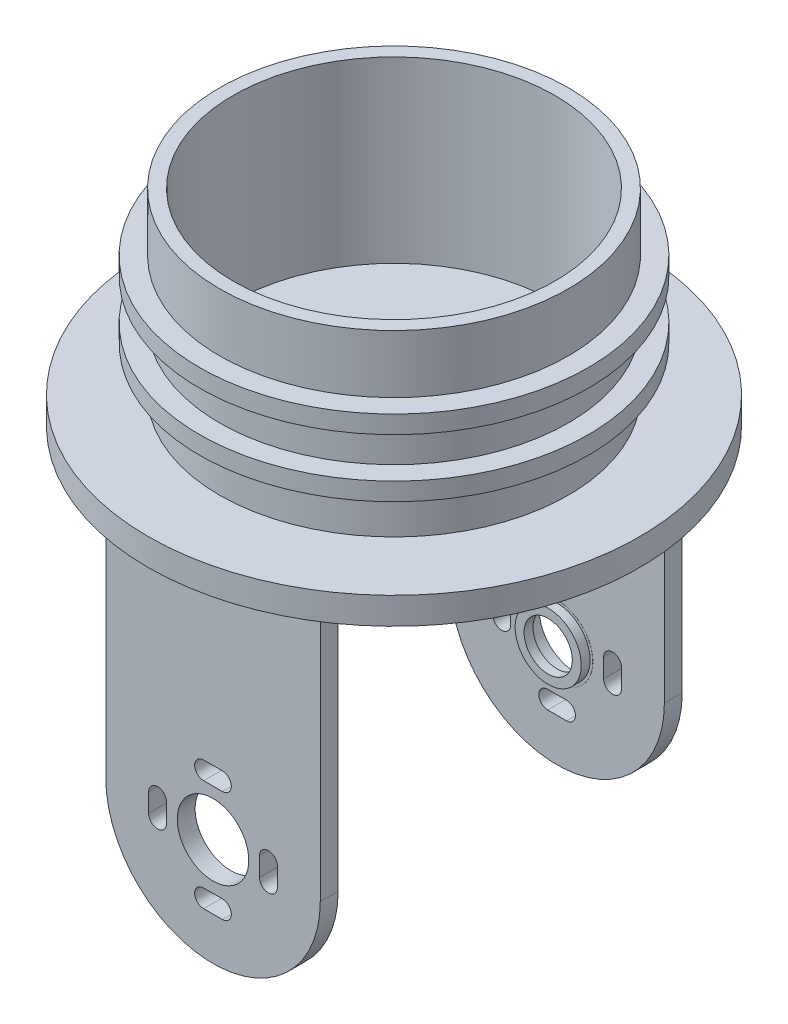
SolidWorks part; units mm, degrees
ref_plane "前基準面" through (0, 0, 0) normal (0, 0, 1) x (1, 0, 0)
ref_plane "上基準面" through (0, 0, 0) normal (0, 1, 0) x (1, 0, 0)
ref_plane "右基準面" through (0, 0, 0) normal (1, 0, 0) x (0, 0, -1)
sketch "草圖1" plane through (0, 0, 0) normal (0, 1, 0) x (1, 0, 0)
  circle A0 centre (0, 0) radius 19.5
  circle A1 centre (0, 0) radius 18
  dimension "D1" = 39
  dimension "D2" = 36
extrude "填料-伸長1" add sketch "草圖1" along normal blind 20
sketch "草圖3" plane through (0, 0, 0) normal (0, -1, 0) x (1, 0, 0)
  circle A0 centre (0, 0) radius 27.5
  dimension "D1" = 55
extrude "填料-伸長2" add sketch "草圖3" along normal blind 3
sketch "草圖4" plane through (0, 0, 0) normal (0, 0, 1) x (1, 0, 0)
  line L0 (0, 20) -> (0, -52.6673) construction
  line L1 (18, 20) -> (-18, 20) construction
  line L2 (-27.5, -3) -> (27.5, -3) construction
  line L3 (-10, -3) -> (10, -3)
  line L4 (-10, -3) -> (-10, -63)
  line L5 (-10, -63) -> (10, -63)
  line L6 (10, -3) -> (10, -63)
  line L8 (-6.5, -28) -> (6.5, -28)
  line L9 (-6.5, -28) -> (-6.5, -53)
  line L10 (-6.5, -53) -> (6.5, -53)
  line L11 (6.5, -28) -> (6.5, -53)
  dimension "D1" = 10
  dimension "D2" = 10
  dimension "D3" = 60
  dimension "D4" = 6.5
  dimension "D5" = 6.5
  dimension "D6" = 25
  dimension "D7" = 25
ref_plane "平面2" through (0, -3, 0) normal (0, -1, 0) x (-1, 0, 0)
ref_plane "平面5" through (0, 0, 0) normal (0, 1, 0) x (1, 0, 0)
ref_plane "平面6" through (0, 7, 0) normal (0, -1, 0) x (-1, 0, 0)
sketch "草圖25" plane through (0, 7, 0) normal (0, -1, 0) x (-1, 0, 0)
  circle A0 centre (0, 0) radius 21.75
  circle A1 centre (0, 0) radius 19.5
  dimension "D1" = 43.5
extrude "填料-伸長12" add sketch "草圖25" along normal blind 2
ref_plane "平面10" through (0, 10.5, 0) normal (0, -1, 0) x (-1, 0, 0)
sketch "草圖26" plane through (0, 10.5, 0) normal (0, -1, 0) x (-1, 0, 0)
  circle A0 centre (0, 0) radius 21.75
  circle A1 centre (0, 0) radius 19.5
extrude "填料-伸長13" add sketch "草圖26" against normal blind 2 from offset 1 offset against normal yes
ref_plane "平面11" through (0, -3, 0) normal (0, -1, 0) x (-1, 0, 0)
sketch "草圖27" plane through (0, -3, 0) normal (0, -1, 0) x (-1, 0, 0)
  line L0 (-27.5, 0) -> (27.5, 0) construction
  line L1 (-12, 20.25) -> (12, 20.25)
  line L2 (-12, 20.25) -> (-12, 18.25)
  line L3 (-12, 18.25) -> (12, 18.25)
  line L4 (12, 20.25) -> (12, 18.25)
  line L5 (-46.0389, 0) -> (46.0389, 0) construction
  line L6 (0, 0) -> (0, -33.56) construction
  line L7 (-12, -18.25) -> (12, -18.25)
  line L8 (12, -20.25) -> (12, -18.25)
  line L9 (-12, -20.25) -> (12, -20.25)
  line L10 (-12, -20.25) -> (-12, -18.25)
  circle A0 centre (0, 0) radius 27.5 construction
  point P13 (-12, 19.25)
  dimension "D1" = 18.25
  dimension "D2" = 24
  dimension "D3" = 12
  dimension "D4" = 2
ref_plane "平面12" through (0, 0, -18.25) normal (0, 0, 1) x (1, 0, 0)
sketch "草圖28" plane through (0, 0, -18.25) normal (0, 0, 1) x (1, 0, 0)
  line L0 (0, -3) -> (0, -48.9232) construction
  line L1 (12, -3) -> (-12, -3) construction
  line L2 (12, -3) -> (-12, -3) construction
  line L3 (-12, -3) -> (12, -3)
  line L4 (-12, -3) -> (-12, -33)
  line L6 (12, -3) -> (12, -33)
  line L7 (-12, -33) -> (12, -33) construction
  line L8 (-1.05, -26.8) -> (1.05, -26.8) construction
  line L9 (-1.05, -25.8) -> (1.05, -25.8)
  line L10 (-1.05, -27.8) -> (1.05, -27.8)
  line L11 (6.2, -31.95) -> (6.2, -34.05) construction
  line L12 (7.2, -31.95) -> (7.2, -34.05)
  line L13 (5.2, -31.95) -> (5.2, -34.05)
  line L14 (-1.05, -39.2) -> (1.05, -39.2) construction
  line L15 (-1.05, -40.2) -> (1.05, -40.2)
  line L16 (-1.05, -38.2) -> (1.05, -38.2)
  line L17 (-6.2, -31.95) -> (-6.2, -34.05) construction
  line L18 (-7.2, -31.95) -> (-7.2, -34.05)
  line L19 (-5.2, -31.95) -> (-5.2, -34.05)
  arc A1 (-12, -33) -> (12, -33) centre (0, -33) ccw
  circle A2 centre (0, -33) radius 4
  arc A3 (-1.05, -25.8) -> (-1.05, -27.8) centre (-1.05, -26.8) ccw
  arc A4 (1.05, -27.8) -> (1.05, -25.8) centre (1.05, -26.8) ccw
  arc A5 (7.2, -31.95) -> (5.2, -31.95) centre (6.2, -31.95) ccw
  arc A6 (5.2, -34.05) -> (7.2, -34.05) centre (6.2, -34.05) ccw
  arc A7 (-1.05, -40.2) -> (-1.05, -38.2) centre (-1.05, -39.2) cw
  arc A8 (1.05, -38.2) -> (1.05, -40.2) centre (1.05, -39.2) cw
  arc A9 (-7.2, -31.95) -> (-5.2, -31.95) centre (-6.2, -31.95) cw
  arc A10 (-5.2, -34.05) -> (-7.2, -34.05) centre (-6.2, -34.05) cw
  point P15 (0, -26.8)
  point P20 (6.2, -33)
  point P32 (0, -39.2)
  point P39 (-6.2, -33)
  dimension "D2" = 0
  dimension "D10" = 8
  dimension "D1" = 30
  dimension "D3" = 0
  dimension "D4" = 6.2
  dimension "D5" = 6.2
  dimension "D6" = 2.1
  dimension "D7" = 2
  dimension "D8" = 2.1
  dimension "D9" = 2
extrude "填料-伸長14" add sketch "草圖28" against normal blind 2
pattern_linear "直線複製排列1" count 2 spacing 38.5 along (0, 0, 1) of "填料-伸長14"
ref_plane "平面13" through (0, 0, 0) normal (0, 1, 0) x (1, 0, 0)
sketch "草圖30" plane through (0, 0, 0) normal (0, 1, 0) x (1, 0, 0)
  line L1 (-5.5, -8.9457) -> (5.5, -8.9457)
  line L2 (-5.5, -8.9457) -> (-5.5, -15.9457)
  line L3 (-5.5, -15.9457) -> (5.5, -15.9457)
  line L4 (5.5, -8.9457) -> (5.5, -15.9457)
sketch "草圖29" plane through (0, 0, 0) normal (0, 1, 0) x (1, 0, 0)
  line L0 (0, 18) -> (0, -18) construction
  line L2 (-4.5, -9.9457) -> (4.5, -9.9457)
  line L3 (-4.5, -9.9457) -> (-4.5, -14.9457)
  line L4 (-4.5, -14.9457) -> (4.5, -14.9457)
  line L5 (4.5, -9.9457) -> (4.5, -14.9457)
  circle A1 centre (0, 0) radius 18 construction
  circle A2 centre (0, 0) radius 18 construction
  dimension "D1" = 4.5
  dimension "D2" = 4.5
  dimension "D3" = 5
extrude "填料-伸長16" add sketch "草圖30" along normal blind 10
extrude "除料-伸長2" cut sketch "草圖29" against normal blind 10 and the other way blind 10
ref_plane "平面14" through (0, 0, -18.25) normal (0, 0, 1) x (1, 0, 0)
sketch "草圖31" plane through (0, 0, -18.25) normal (0, 0, 1) x (1, 0, 0)
  circle A0 centre (0, -33) radius 3.7
  circle A1 centre (0, -33) radius 2.7
  dimension "D1" = 7.4
  dimension "D2" = 5.4
extrude "填料-伸長17" add sketch "草圖31" along normal blind 1 separate body
sketch "草圖32" plane through (0, 0, -18.25) normal (0, 0, 1) x (1, 0, 0)
  circle A0 centre (0, -33) radius 3.7
  circle A1 centre (0, -33) radius 4
extrude "填料-伸長18" add sketch "草圖32" along normal blind 0.01
sketch "草圖33" plane through (0, 0, -20.25) normal (0, 0, -1) x (-1, 0, 0)
  line L0 (-12, -3) -> (12, -3) construction
  circle A0 centre (0, -10.5) radius 6.3
  circle A1 centre (0, -10.5) radius 4.8
  dimension "D1" = 12.6
  dimension "D2" = 9.6
  dimension "D3" = 7.5
extrude "填料-伸長19" add sketch "草圖33" along normal blind 10.5
sketch "草圖35" plane through (0, 0, -20.25) normal (0, 0, -1) x (-1, 0, 0)
  circle A0 centre (0, -10.5) radius 4.8
extrude "除料-伸長3" cut sketch "草圖35" against normal blind 8
sketch "草圖36" plane through (0, 0, -30.75) normal (0, 0, -1) x (-1, 0, 0)
  line L0 (0, 0) -> (0, -38.2) construction
  line L1 (-1.05, -38.2) -> (1.05, -38.2) construction
  line L3 (-1, -14.0734) -> (1, -14.0734)
  line L4 (-1, -14.0734) -> (-1, -17.953)
  line L5 (-1, -17.953) -> (1, -17.953)
  line L6 (1, -14.0734) -> (1, -17.953)
  dimension "D1" = 1
  dimension "D2" = 1
extrude "除料-伸長4" cut sketch "草圖36" against normal blind 3
